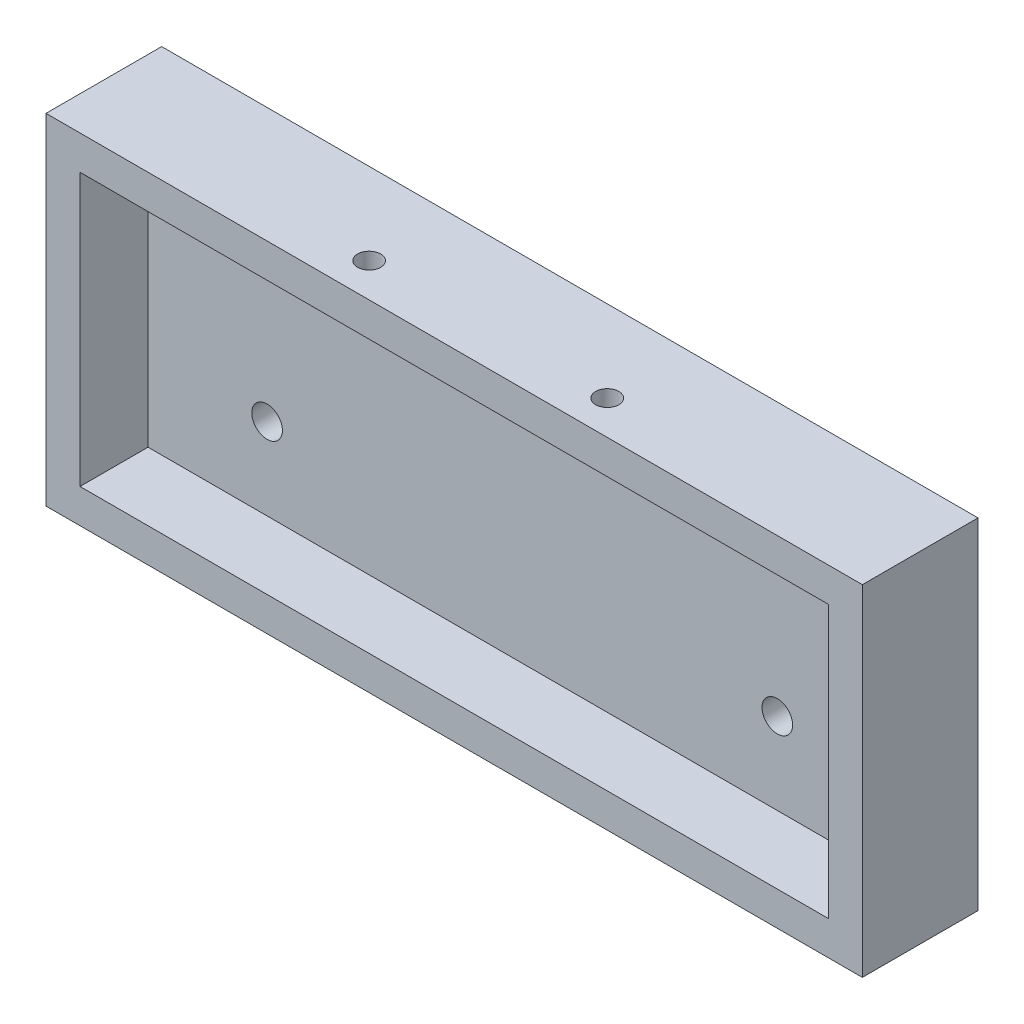
SolidWorks part; units mm, degrees
ref_plane "Front Plane" through (0, 0, 0) normal (0, 0, 1) x (1, 0, 0)
ref_plane "Top Plane" through (0, 0, 0) normal (0, 1, 0) x (1, 0, 0)
ref_plane "Right Plane" through (0, 0, 0) normal (1, 0, 0) x (0, 0, -1)
sketch "Sketch2" plane through (0, 0, 0) normal (0, 0, 1) x (1, 0, 0)
  line L1 (0, 0) -> (120, 0)
  line L2 (0, 0) -> (0, 50)
  line L3 (0, 50) -> (120, 50)
  line L4 (120, 0) -> (120, 50)
  dimension "D1" = 120
  dimension "D2" = 50
extrude "Boss-Extrude3" add sketch "Sketch2" along normal blind 17
sketch "Sketch4" plane through (0, 0, 17) normal (0, 0, 1) x (1, 0, 0)
  line L0 (120, 50) -> (0, 50) construction
  line L1 (5, 45) -> (115, 45)
  line L2 (5, 45) -> (5, 5)
  line L3 (5, 5) -> (115, 5)
  line L4 (115, 45) -> (115, 5)
  line L5 (0, 0) -> (120, 0) construction
  line L6 (0, 50) -> (0, 0) construction
  line L7 (120, 0) -> (120, 50) construction
  dimension "D1" = 5
  dimension "D2" = 5
  dimension "D3" = 5
  dimension "D4" = 5
extrude "Cut-Extrude1" cut sketch "Sketch4" against normal blind 10
sketch "Sketch7" plane through (0, 45, 0) normal (0, -1, 0) x (1, 0, 0)
  line L0 (115, 7) -> (5, 7) construction
  line L1 (5, 7) -> (5, 17) construction
  line L2 (115, 7) -> (115, 17) construction
  point P0 (77.5, 12)
  point P1 (42.5, 12)
  point P6 (0, 0)
  dimension "D1" = 35
  dimension "D2" = 5
  dimension "D3" = 37.5
  dimension "D4" = 37.5
hole_wizard "CSK for M3 Flat Head Machine Screw1" positions "Sketch8" profile "Sketch9" countersink size "M3" standard "ANSI Metric"
sketch "Sketch8" plane through (0, 45, 0) normal (0, -1, 0) x (-1, 0, 0)
  point P0 (-42.5, -12)
  point P3 (-77.5, -12)
sketch "Sketch9" plane through (42.5, 45, 12) normal (1, 0, 0) x (0, 0, -1)
  line L0 (0, 0) -> (0, 5)
  line L1 (0, 5) -> (1.7, 5)
  line L2 (1.7, 5) -> (1.7, 1.45)
  line L3 (1.7, 1.45) -> (3.15, 0)
  line L5 (3.15, 0) -> (0, 0)
  line L6 (-1.7, 1.45) -> (-3.15, 0) construction
  line L11 (0, -6.35) -> (0, 107.95) construction
  dimension "Thru Hole Dia." = 3.4
  dimension "Thru Hole Depth" = 5
  dimension "Near C'Sink Dia." = 6.3
  dimension "Near C'Sink Angle" = 90
sketch "Sketch10" plane through (0, 0, 7) normal (0, 0, 1) x (1, 0, 0)
  line L4 (5, 45) -> (5, 5) construction
  line L5 (115, 5) -> (115, 45) construction
  line L6 (5, 5) -> (115, 5) construction
  point P0 (22.5, 17)
  point P1 (97.5, 17)
  point P2 (0, 0)
  point P5 (0, 0)
  dimension "D1" = 75
  dimension "D2" = 17.5
  dimension "D3" = 17.5
  dimension "D4" = 12
hole_wizard "CSK for M4 Flat Head Machine Screw3" positions "Sketch11" profile "Sketch12" countersink size "M4" standard "ANSI Metric" end condition through all
sketch "Sketch11" plane through (0, 0, 0) normal (0, 0, -1) x (-1, 0, 0)
  point P0 (-97.5, 17)
  point P3 (-22.5, 17)
sketch "Sketch12" plane through (97.5, 17, 0) normal (1, 0, 0) x (0, 1, 0)
  line L0 (0, 0) -> (0, 17)
  line L1 (0, 17) -> (2.25, 17)
  line L2 (2.25, 17) -> (2.25, 2.45)
  line L3 (2.25, 2.45) -> (4.7, 0)
  line L5 (4.7, 0) -> (0, 0)
  line L6 (-2.25, 2.45) -> (-4.7, 0) construction
  line L11 (0, -6.35) -> (0, 107.95) construction
  dimension "Thru Hole Dia." = 4.5
  dimension "Thru Hole Depth" = 17
  dimension "Near C'Sink Dia." = 9.4
  dimension "Near C'Sink Angle" = 90
